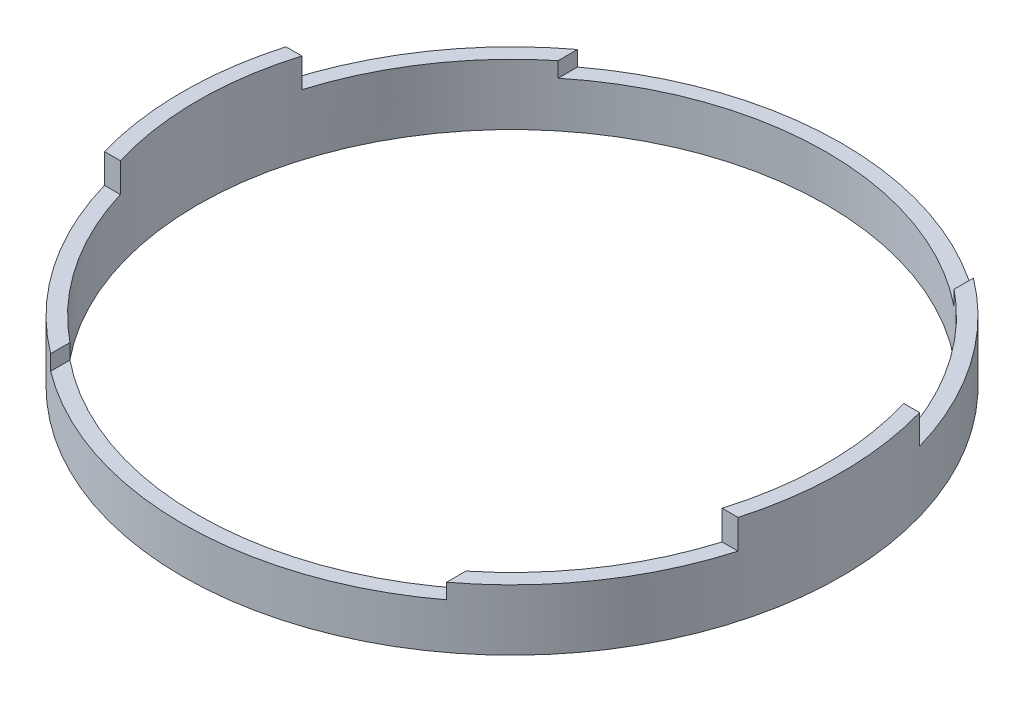
SolidWorks part; units mm, degrees
ref_plane "Front Plane" through (0, 0, 0) normal (0, 0, 1) x (1, 0, 0)
ref_plane "Top Plane" through (0, 0, 0) normal (0, 1, 0) x (1, 0, 0)
ref_plane "Right Plane" through (0, 0, 0) normal (1, 0, 0) x (0, 0, -1)
sketch "Sketch1" plane through (0, 0, 0) normal (0, 1, 0) x (1, 0, 0)
  circle A0 centre (0, 0) radius 65.532
  circle A1 centre (0, 0) radius 68.707
  dimension "D1" = 131.064
  dimension "D2" = 3.175
extrude "Boss-Extrude1" add sketch "Sketch1" along normal mid plane 12.7
sketch "Sketch2" plane through (0, 6.35, 0) normal (0, 1, 0) x (1, 0, 0)
  line L0 (-41.275, -45.72) -> (41.275, -45.72) construction
  line L1 (-41.275, -50.9001) -> (-41.275, -54.9275)
  line L2 (41.275, -50.9001) -> (41.275, -54.9275)
  arc A0 (-41.275, -50.9001) -> (41.275, -50.9001) centre (0, 0) ccw
  arc A1 (-41.275, -54.9275) -> (41.275, -54.9275) centre (0, 0) ccw
  circle A2 centre (0, 0) radius 65.532 construction
  circle A3 centre (0, 0) radius 68.707 construction
  circle A4 centre (0, 0) radius 61.595 construction
  dimension "D1" = 123.19
  dimension "D2" = 82.55
extrude "Cut-Extrude1" cut sketch "Sketch2" against normal blind 3.175
mirror "Mirror1" about plane through (0, 0, 0) normal (0, 0, 1) of "Cut-Extrude1"
sketch "Sketch3" [suppressed] plane through (0, 6.35, 0) normal (0, 1, 0) x (1, 0, 0)
  line L0 (-62.6633, 19.177) -> (-62.6633, -19.177) construction
  line L1 (-62.6633, -19.177) -> (-65.9765, -19.177)
  line L2 (-62.6633, 19.177) -> (-65.9765, 19.177)
  line L3 (-55, 0) -> (55, 0) construction
  arc A0 (-62.6633, 19.177) -> (-62.6633, -19.177) centre (0, 0) ccw
  arc A1 (-65.9765, 19.177) -> (-65.9765, -19.177) centre (0, 0) ccw
  arc A2 (-39.37, 52.3875) -> (-39.37, -52.3875) centre (0, 0) ccw construction
  arc A3 (-39.37, 56.3086) -> (-39.37, -56.3086) centre (0, 0) ccw construction
  point P12 (-62.6633, 0)
  dimension "D1" = 38.354
extrude "Cut-Extrude2" [suppressed] cut sketch "Sketch3" against normal blind 6.604
mirror "Mirror2" [suppressed] about plane through (0, 0, 0) normal (1, 0, 0)
sketch "Sketch4" plane through (0, 6.35, 0) normal (0, 1, 0) x (1, 0, 0)
  line L0 (-62.7404, 18.923) -> (-62.7404, -18.923) construction
  line L1 (-6.985, 0) -> (6.985, 0) construction
  line L2 (-62.7404, 18.923) -> (-66.0498, 18.923)
  line L3 (-62.7404, -18.923) -> (-66.0498, -18.923)
  arc A0 (-62.7404, 18.923) -> (-62.7404, -18.923) centre (0, 0) ccw
  arc A1 (-66.0498, 18.923) -> (-66.0498, -18.923) centre (0, 0) ccw
  arc A2 (-41.275, 54.9275) -> (-41.275, -54.9275) centre (0, 0) ccw construction
  arc A3 (-41.275, 50.9001) -> (-41.275, -50.9001) centre (0, 0) ccw construction
  point P12 (-62.7404, 0)
  dimension "D1" = 37.846
extrude "Boss-Extrude2" add sketch "Sketch4" along normal blind 6.096
mirror "Mirror3" about plane through (0, 0, 0) normal (1, 0, 0) of "Boss-Extrude2"
